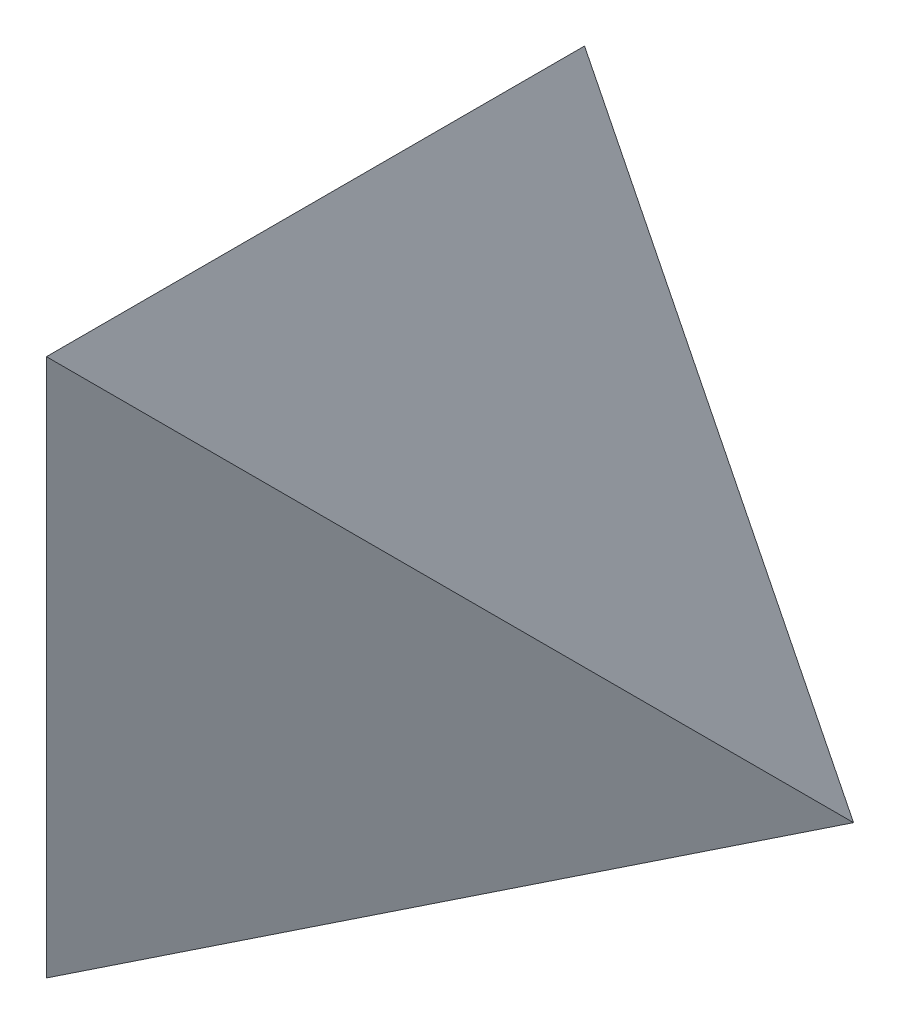
SolidWorks part; units mm, degrees
ref_plane "Front" through (0, 0, 0) normal (0, 0, 1) x (1, 0, 0)
ref_plane "Top" through (0, 0, 0) normal (0, 1, 0) x (1, 0, 0)
ref_plane "Right" through (0, 0, 0) normal (1, 0, 0) x (0, 0, -1)
sketch "Sketch1" plane through (0, 0, 0) normal (0, 1, 0) x (1, 0, 0)
  line L1 (-2, -2) -> (2, -2)
  line L2 (-2, -2) -> (-2, 2)
  line L3 (-2, 2) -> (2, 2)
  line L4 (2, -2) -> (2, 2)
  line L5 (-2, -2) -> (2, 2) construction
  line L6 (-2, 2) -> (2, -2) construction
  point P0 (0, 0)
  dimension "D1" = 4
  dimension "D2" = 4
extrude "Boss-Extrude1" add sketch "Sketch1" along normal blind 4
sketch3d "3DSketch1"
  line L0 (0, 4, -2) -> (-2, 0, -2)
  line L1 (2, 4, -2) -> (-2, 4, -2) construction
  line L2 (-2, 0, -2) -> (0, 0, 2)
  line L3 (-2, 0, 2) -> (2, 0, 2) construction
  line L4 (0, 0, 2) -> (0, 4, -2)
extrude "Cut-Extrude1" cut sketch "3DSketch1" along direction (0, -1, 0) on the side against the normal blind 10
sketch "Sketch2" plane through (0, 0, 2) normal (0, 0, 1) x (1, 0, 0)
  line L0 (0, 4) -> (2, 0)
  line L5 (2, 4) -> (0, 4)
  line L6 (0, 4) -> (0, 0)
  line L7 (0, 0) -> (2, 0)
  line L8 (2, 0) -> (2, 4)
  line L9 (2, 4) -> (0, 4)
  line L10 (0, 4) -> (0, 0)
  line L11 (0, 0) -> (2, 0)
  line L12 (2, 0) -> (2, 4)
  line M5 (2, 4) -> (0, 4)
  line M8 (2, 0) -> (2, 4)
  dimension "D1" = 0
extrude "Cut-Extrude2" cut sketch "Sketch2" against normal blind 10 contours L0 M5 M8
sketch "Sketch3" plane through (0, 0, 0) normal (0, -1, 0) x (1, 0, 0)
  line L0 (0, 2) -> (2, -2)
  line L5 (0, 2) -> (0, -2)
  line L6 (2, 2) -> (0, 2)
  line L7 (2, -2) -> (2, 2)
  line L8 (0, -2) -> (2, -2)
  line L9 (0, 2) -> (0, -2)
  line L10 (2, 2) -> (0, 2)
  line L11 (2, -2) -> (2, 2)
  line L12 (0, -2) -> (2, -2)
  line M6 (2, 2) -> (0, 2)
  line M9 (2, -2) -> (2, 2)
  dimension "D1" = 0
extrude "Cut-Extrude3" cut sketch "Sketch3" against normal blind 10 contours L0 M6 M9
